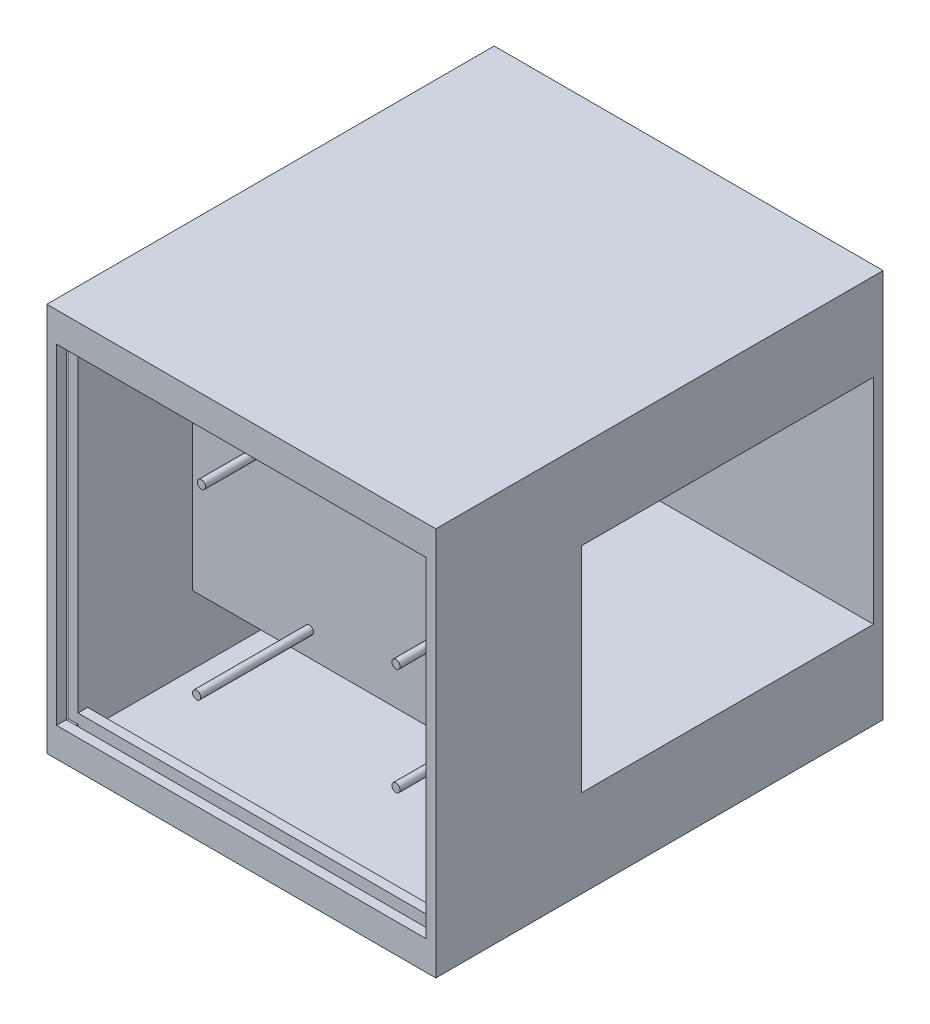
SolidWorks part; units mm, degrees
ref_plane "Front Plane" through (0, 0, 0) normal (0, 0, 1) x (1, 0, 0)
ref_plane "Top Plane" through (0, 0, 0) normal (0, 1, 0) x (1, 0, 0)
ref_plane "Right Plane" through (0, 0, 0) normal (1, 0, 0) x (0, 0, -1)
sketch "Sketch1" plane through (0, 0, 0) normal (0, 0, 1) x (1, 0, 0)
  line L1 (0, 0) -> (101.6, 0)
  line L2 (0, 0) -> (0, -101.6)
  line L3 (0, -101.6) -> (101.6, -101.6)
  line L4 (101.6, 0) -> (101.6, -101.6)
  dimension "D1" = 101.6
  dimension "D2" = 101.6
extrude "Boss-Extrude2" add sketch "Sketch1" along normal blind 116.84
sketch "Sketch2" plane through (101.6, 0, 0) normal (1, 0, 0) x (0, 0, -1)
  line L0 (-40.64, -78.74) -> (-40.64, -101.6) construction
  line L1 (-2.54, -22.86) -> (-78.74, -22.86)
  line L2 (-2.54, -22.86) -> (-2.54, -78.74)
  line L3 (-2.54, -78.74) -> (-78.74, -78.74)
  line L4 (-78.74, -22.86) -> (-78.74, -78.74)
  line L5 (-116.84, -101.6) -> (0, -101.6) construction
  line L6 (-40.64, -22.86) -> (-40.64, 0) construction
  line L7 (-116.84, 0) -> (0, 0) construction
  line L8 (-2.54, -50.8) -> (0, -50.8) construction
  line L9 (0, -101.6) -> (0, 0) construction
  dimension "D1" = 2.54
  dimension "D2" = 76.2
  dimension "D4" = 55.88
extrude "Cut-Extrude1" cut sketch "Sketch2" against normal blind 99.06
ref_plane "Plane3" through (99.06, 0, 0) normal (1, 0, 0) x (0, 0, -1)
sketch "Sketch3" plane through (99.06, 0, 0) normal (1, 0, 0) x (0, 0, -1)
  line L0 (0, -101.6) -> (0, 0) construction
  line L1 (-2.54, -81.28) -> (-114.3, -81.28)
  line L2 (-2.54, -81.28) -> (-2.54, -99.06)
  line L3 (-2.54, -99.06) -> (-114.3, -99.06)
  line L4 (-114.3, -81.28) -> (-114.3, -99.06)
  line L5 (-116.84, -101.6) -> (-116.84, 0) construction
  line L6 (-116.84, -101.6) -> (0, -101.6) construction
  line L7 (-78.74, -78.74) -> (-2.54, -78.74) construction
  line L8 (-2.54, -20.32) -> (-114.3, -20.32)
  line L9 (-114.3, -2.54) -> (-114.3, -20.32)
  line L10 (-2.54, -2.54) -> (-114.3, -2.54)
  line L11 (-2.54, -2.54) -> (-2.54, -20.32)
  line L12 (-2.54, -99.06) -> (-2.54, -20.32) construction
  line L15 (-116.84, 0) -> (0, 0) construction
  dimension "D1" = 2.54
  dimension "D2" = 2.54
  dimension "D3" = 2.54
  dimension "D4" = 2.54
  dimension "D6" = 2.54
  dimension "D5" = 2
extrude "Cut-Extrude2" cut sketch "Sketch3" against normal blind 96.52 contours L3 L4 L1 L2 | L8 L9 L10 L11
sketch "Sketch4" plane through (0, 0, 116.84) normal (0, 0, 1) x (1, 0, 0)
  line L1 (101.6, -101.6) -> (101.6, 0) construction
  line L2 (0, 0) -> (0, -101.6) construction
  line L3 (101.6, 0) -> (0, 0) construction
  line L4 (2.54, -2.54) -> (99.06, -2.54)
  line L5 (2.54, -2.54) -> (2.54, -99.06)
  line L6 (2.54, -99.06) -> (99.06, -99.06)
  line L7 (99.06, -2.54) -> (99.06, -99.06)
  line L8 (0, -101.6) -> (101.6, -101.6) construction
  dimension "D1" = 2.54
  dimension "D2" = 2.54
  dimension "D3" = 2.54
  dimension "D4" = 2.54
extrude "Cut-Extrude3" cut sketch "Sketch4" against normal blind 35.56
sketch "Sketch5" plane through (0, 0, 81.28) normal (0, 0, 1) x (1, 0, 0)
  line L0 (87.63, -77.47) -> (87.63, -24.13) construction
  line L4 (87.63, -77.47) -> (19.05, -77.47) construction
  line L5 (87.63, -24.13) -> (19.05, -24.13) construction
  line L6 (19.05, -24.13) -> (19.05, -77.47) construction
  line L7 (2.54, -2.54) -> (2.54, -99.06) construction
  circle A0 centre (85.09, -41.91) radius 1.0795
  circle A1 centre (85.09, -69.85) radius 1.0795
  circle A2 centre (34.29, -26.67) radius 1.0795
  circle A3 centre (33.02, -74.93) radius 1.0795
  dimension "D4" = 2.54
  dimension "D5" = 7.62
  dimension "D6" = 2.54
  dimension "D8" = 2.54
  dimension "D10" = 2.54
  dimension "D1" = 53.34
  dimension "D2" = 16.51
  dimension "D3" = 68.58
  dimension "D7" = 27.94
  dimension "D9" = 15.24
  dimension "D11" = 13.97
extrude "Boss-Extrude3" add sketch "Sketch5" along normal blind 29.464
sketch "Sketch8" plane through (0, 0, 0) normal (-1, 0, 0) x (0, 0, 1)
  line L0 (116.84, 0) -> (116.84, -101.6) construction
  line L1 (114.3, -5.08) -> (111.252, -5.08)
  line L2 (114.3, -5.08) -> (114.3, -96.52)
  line L3 (114.3, -96.52) -> (111.252, -96.52)
  line L4 (111.252, -5.08) -> (111.252, -96.52)
  line L5 (116.84, 0) -> (0, 0) construction
  line L6 (116.84, -101.6) -> (0, -101.6) construction
  dimension "D1" = 3.048
  dimension "D2" = 2.54
  dimension "D3" = 5.08
  dimension "D4" = 5.08
extrude "Cut-Extrude4" cut sketch "Sketch8" against normal blind 2.54
sketch "Sketch10" plane through (2.54, 0, 0) normal (1, 0, 0) x (0, 0, -1)
  line L0 (-114.3, -96.52) -> (-114.3, -5.08) construction
  line L1 (-116.84, -99.06) -> (-114.3, -99.06)
  line L2 (-116.84, -99.06) -> (-116.84, -93.98)
  line L3 (-116.84, -93.98) -> (-114.3, -93.98)
  line L4 (-114.3, -99.06) -> (-114.3, -93.98)
  line L6 (-2.54, -99.06) -> (-116.84, -99.06) construction
  line L7 (-111.252, -99.06) -> (-108.712, -99.06)
  line L8 (-111.252, -99.06) -> (-111.252, -93.98)
  line L9 (-111.252, -93.98) -> (-108.712, -93.98)
  line L12 (-116.84, -2.54) -> (-114.3, -2.54)
  line L13 (-116.84, -2.54) -> (-116.84, -7.7389)
  line L14 (-116.84, -7.7389) -> (-114.3, -7.7389)
  line L15 (-114.3, -2.54) -> (-114.3, -7.7389)
  line L16 (-2.54, -2.54) -> (-116.84, -2.54) construction
  line L17 (-111.252, -2.54) -> (-108.712, -2.54)
  line L18 (-111.252, -2.54) -> (-111.252, -7.62)
  line L19 (-111.252, -7.62) -> (-108.712, -7.62)
  line L20 (-108.712, -99.06) -> (-108.712, -93.98)
  line L21 (-116.84, -101.6) -> (-116.84, 0) construction
  line L22 (-108.712, -2.54) -> (-108.712, -7.62)
  dimension "D1" = 5.588
  dimension "D2" = 2.54
  dimension "D3" = 5.1989
  dimension "D4" = 5.588
  dimension "D5" = 5.08
  dimension "D6" = 2.54
  dimension "D7" = 5.08
  dimension "D8" = 5.08
extrude "Boss-Extrude4" add sketch "Sketch10" along normal blind 96.52
